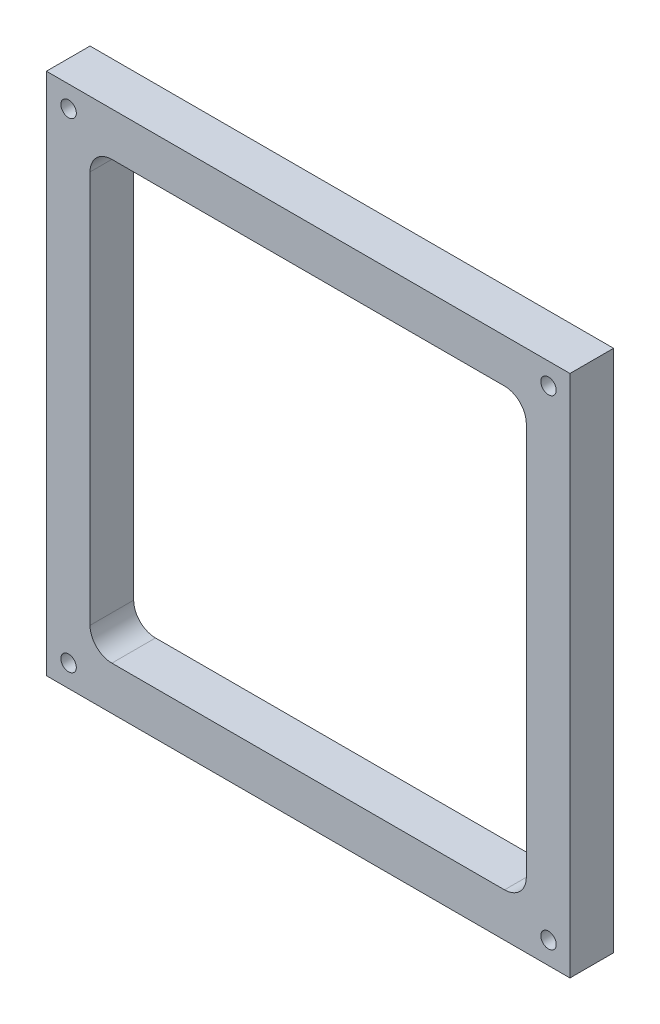
SolidWorks part; units mm, degrees
ref_plane "Front Plane" through (0, 0, 0) normal (0, 0, 1) x (1, 0, 0)
ref_plane "Top Plane" through (0, 0, 0) normal (0, 1, 0) x (1, 0, 0)
ref_plane "Right Plane" through (0, 0, 0) normal (1, 0, 0) x (0, 0, -1)
sketch "Sketch1" plane through (0, 0, 0) normal (0, 0, 1) x (1, 0, 0)
  line L1 (-61.1427, 80.0484) -> (91.2573, 80.0484)
  line L2 (-61.1427, 80.0484) -> (-61.1427, -72.3516)
  line L3 (-61.1427, -72.3516) -> (91.2573, -72.3516)
  line L4 (91.2573, 80.0484) -> (91.2573, -72.3516)
  line L5 (-42.0927, 67.3484) -> (72.2073, 67.3484)
  line L6 (-48.4427, 60.9984) -> (-48.4427, -53.3016)
  line L7 (-42.0927, -59.6516) -> (72.2073, -59.6516)
  line L8 (78.5573, 60.9984) -> (78.5573, -53.3016)
  arc A0 (-48.4427, 60.9984) -> (-42.0927, 67.3484) centre (-42.0927, 60.9984) cw
  arc A1 (72.2073, 67.3484) -> (78.5573, 60.9984) centre (72.2073, 60.9984) cw
  arc A2 (-42.0927, -59.6516) -> (-48.4427, -53.3016) centre (-42.0927, -53.3016) cw
  arc A3 (72.2073, -59.6516) -> (78.5573, -53.3016) centre (72.2073, -53.3016) ccw
  point P8 (15.0573, 67.3484)
  point P9 (15.0573, 80.0484)
  point P10 (78.5573, 3.8484)
  point P11 (91.2573, 3.8484)
  dimension "D4" = 6.35
  dimension "D1" = 152.4
  dimension "D2" = 152.4
  dimension "D3" = 12.7
  dimension "D5" = 12.7
extrude "Boss-Extrude1" add sketch "Sketch1" along normal blind 12.7
hole_wizard "#8 Clearance Hole2" positions "Sketch2" profile "Sketch3" hole size "#8" standard "ANSI Inch" end condition through all
sketch "Sketch2" plane through (0, 0, 12.7) normal (0, 0, 1) x (1, 0, 0)
  line L0 (-61.1427, 72.3807) -> (-54.6879, 72.3807)
  line L1 (-61.1427, 80.0484) -> (-61.1427, -72.3516) construction
  line L3 (-54.6879, 80.0484) -> (-54.6879, 73.7958)
  line L4 (91.2573, 80.0484) -> (-61.1427, 80.0484) construction
  point P8 (-54.6879, 73.7958)
sketch "Sketch3" plane through (-54.6879, 73.7958, 12.7) normal (1, 0, 0) x (0, -1, 0)
  line L0 (0, 0) -> (0, 12.7)
  line L1 (0, 12.7) -> (2.2479, 12.7)
  line L2 (2.2479, 12.7) -> (2.2479, 0)
  line L5 (2.2479, 0) -> (0, 0)
  line L11 (0, -6.35) -> (0, 107.95) construction
  dimension "Thru Hole Dia." = 4.4958
  dimension "Thru Hole Depth" = 12.7
pattern_linear "LPattern1" count 2 spacing 139.7 along (1, 0, 0) count 2 spacing 139.7 along (0, -1, 0) of "#8 Clearance Hole2"
